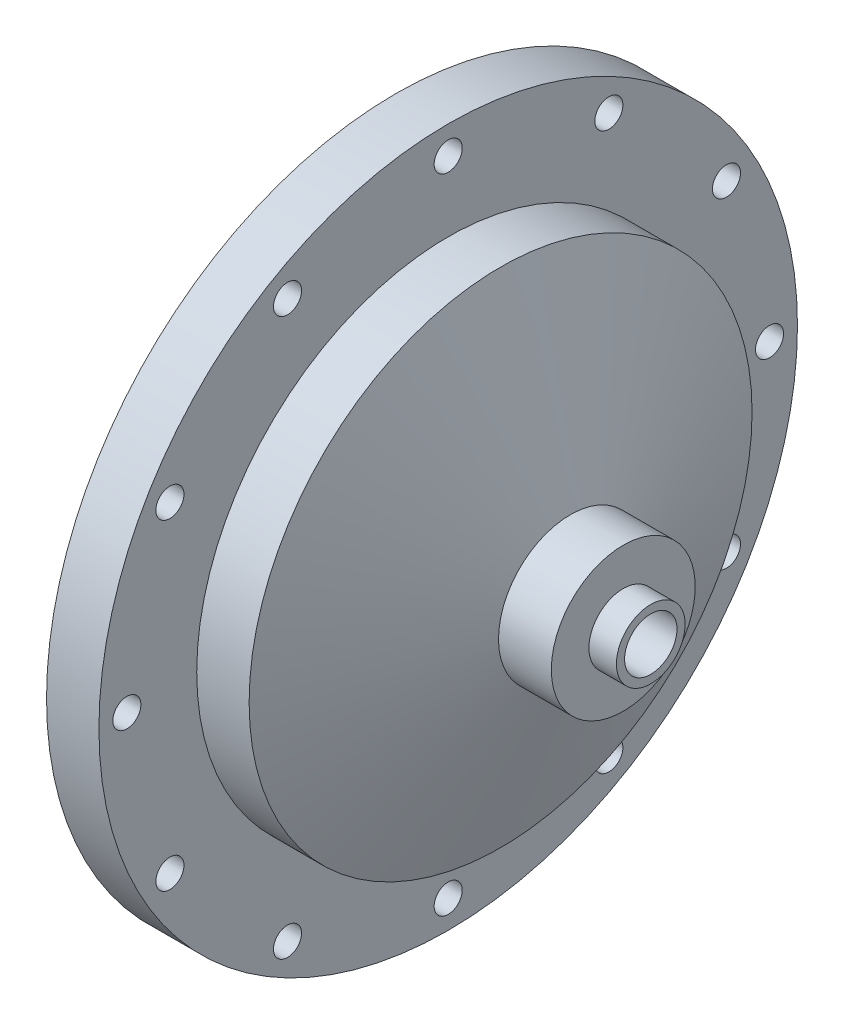
SolidWorks part; units mm, degrees
material "7075-T6 (SN)"
ref_plane "Front Plane" through (0, 0, 0) normal (0, 0, 1) x (1, 0, 0)
ref_plane "Top Plane" through (0, 0, 0) normal (0, 1, 0) x (1, 0, 0)
ref_plane "Right Plane" through (0, 0, 0) normal (1, 0, 0) x (0, 0, -1)
sketch "Sketch2" plane through (0, 0, 0) normal (0, 0, 1) x (1, 0, 0)
  line L0 (0, 0) -> (165.0115, 0) construction
  line L1 (0, 0) -> (0, 63.5)
  line L2 (0, 63.5) -> (9.525, 63.5)
  line L4 (19.05, 45.72) -> (31.75, 13.081)
  line L5 (41.355, 13.081) -> (41.355, 6.2484)
  line L6 (31.75, 13.081) -> (41.355, 13.081)
  line L7 (41.355, 6.2484) -> (46.355, 6.2484)
  line L8 (46.355, 6.2484) -> (46.355, 0)
  line L9 (0, 0) -> (46.355, 0)
  line L11 (19.05, 45.72) -> (9.525, 45.72)
  line L14 (9.525, 45.72) -> (9.525, 63.5)
  dimension "D1" = 63.5
  dimension "D2" = 9.525
  dimension "D3" = 45.72
  dimension "D4" = 13.081
  dimension "D5" = 12.7
  dimension "D7" = 6.2484
  dimension "D8" = 5
  dimension "D9" = 9.525
  dimension "D10" = 46.355
revolve "Main Structure" add sketch "Sketch2" angle 360 about L0
cosmetic thread "Cosmetic Thread1" parameters "D2"=23.1953
sketch "Sketch3" plane through (46.355, 0, 0) normal (1, 0, 0) x (0, 0, -1)
  circle A0 centre (0, 0) radius 4.7625
  dimension "D1" = 9.525
extrude "Oxidizer Inlet Hole" cut sketch "Sketch3" against normal through all
sketch "Sketch4" plane through (0, 0, 0) normal (-1, 0, 0) x (0, 0, 1)
  circle A0 centre (0, 0) radius 58.42 construction
  circle A1 centre (0, -58.42) radius 2.146
  circle A2 centre (-29.21, -50.5932) radius 2.146
  circle A3 centre (-50.5932, -29.21) radius 2.146
  circle A4 centre (-58.42, 0) radius 2.146
  circle A5 centre (-50.5932, 29.21) radius 2.146
  circle A6 centre (-29.21, 50.5932) radius 2.146
  circle A7 centre (0, 58.42) radius 2.146
  circle A8 centre (29.21, 50.5932) radius 2.146
  circle A9 centre (50.5932, 29.21) radius 2.146
  circle A10 centre (58.42, 0) radius 2.146
  circle A11 centre (50.5932, -29.21) radius 2.146
  circle A12 centre (29.21, -50.5932) radius 2.146
  point P29 (0, 0)
  dimension "D1" = 12
  dimension "D2" = 116.84
hole_wizard "Flange Holes" positions "Sketch7" profile "Sketch8" hole size "#7" standard "ANSI Inch" end condition up to next
sketch "Sketch7" plane through (0, 0, 0) normal (-1, 0, 0) x (0, 0, 1)
  point P0 (0, -58.42)
  point P3 (-29.21, -50.5932)
  point P6 (-50.5932, -29.21)
  point P9 (-58.42, 0)
  point P12 (-50.5932, 29.21)
  point P15 (-29.21, 50.5932)
  point P18 (0, 58.42)
  point P21 (29.21, 50.5932)
  point P24 (50.5932, 29.21)
  point P27 (58.42, 0)
  point P30 (50.5932, -29.21)
  point P33 (29.21, -50.5932)
sketch "Sketch8" plane through (0, -58.42, 0) normal (0, 1, 0) x (0, 0, 1)
  line L0 (0, 0) -> (0, 9.525)
  line L1 (0, 9.525) -> (2.5527, 9.525)
  line L2 (2.5527, 9.525) -> (2.5527, 0)
  line L5 (2.5527, 0) -> (0, 0)
  line L11 (0, -6.35) -> (0, 107.95) construction
  dimension "Thru Hole Dia." = 5.1054
  dimension "Thru Hole Depth" = 9.525
sketch "Sketch9" plane through (0, 0, 0) normal (-1, 0, 0) x (0, 0, 1)
  line L0 (0, 0) -> (-67.6727, 18.1329) construction
  line L1 (0, 0) -> (-58.42, 0) construction
  circle A0 centre (0, 0) radius 58.42 construction
  circle A1 centre (-56.4294, 15.1202) radius 2.9451
  circle A2 centre (56.4294, -15.1202) radius 2.9451
  point P14 (0, 0)
  dimension "D1" = 15
  dimension "D2" = 2
hole_wizard "Dowel Holes" positions "Sketch10" profile "Sketch11" hole size "3/16" standard "ANSI Inch"
sketch "Sketch10" plane through (0, 0, 0) normal (-1, 0, 0) x (0, 0, 1)
  point P0 (56.4294, -15.1202)
  point P3 (-56.4294, 15.1202)
sketch "Sketch11" plane through (0, -15.1202, 56.4294) normal (0, 1, 0) x (0, 0, 1)
  line L0 (0, 0) -> (0, 7.7808)
  line L1 (0, 7.7808) -> (2.3812, 6.35)
  line L2 (2.3812, 6.35) -> (2.3812, 0)
  line L5 (2.3812, 0) -> (0, 0)
  line L10 (0, 7.7808) -> (-2.3812, 6.35) construction
  line L11 (0, -6.35) -> (0, 107.95) construction
  dimension "Hole Dia." = 4.7625
  dimension "Hole Depth" = 6.35
  dimension "Drill Angle" = 118
sketch "Sketch12" plane through (0, 0, 0) normal (-1, 0, 0) x (0, 0, 1)
  circle A0 centre (0, 0) radius 38.1
  dimension "D1" = 76.2
extrude "Impinging Plate Flat Cut" cut sketch "Sketch12" against normal blind 3.81
ref_plane "Plane1" through (6.35, 0, 0) normal (-1, 0, 0) x (0, 0, 1)
sketch "Sketch14" plane through (3.81, 0, 0) normal (-1, 0, 0) x (0, 0, 1)
  circle A0 centre (0, 0) radius 38.1
  dimension "D1" = 76.2
sketch "Sketch15" plane through (6.35, 0, 0) normal (-1, 0, 0) x (0, 0, 1)
  circle A0 centre (0, 0) radius 38.1
  dimension "D1" = 76.2
ref_plane "Plane4" through (15.875, 0, 0) normal (-1, 0, 0) x (0, 0, 1)
loft "Impinging Plate Taper Cut" cut profiles "Sketch14", "Sketch15"
sketch "Sketch16" plane through (15.875, 0, 0) normal (-1, 0, 0) x (0, 0, 1)
  circle A0 centre (0, 0) radius 28.575
  dimension "D1" = 57.15
ref_plane "Plane2" through (31.115, 0, 0) normal (-1, 0, 0) x (0, 0, 1)
sketch "Sketch17" plane through (31.115, 0, 0) normal (-1, 0, 0) x (0, 0, 1)
  circle A0 centre (0, 0) radius 4.7625
  dimension "D1" = 9.525
loft "Internal Flow Path Loft Cut" cut profiles "Sketch16", "Sketch17"
sketch "Sketch21" plane through (6.35, 0, 0) normal (-1, 0, 0) x (0, 0, 1)
  circle A0 centre (0, 0) radius 28.575
  dimension "D1" = 57.15
extrude "Cut-Extrude1" cut sketch "Sketch21" against normal blind 9.525
fillet "Internal Fillet" radius 3.175 1 edges at (31.115, 0, 4.7625)
sketch "Sketch18" plane through (6.35, 0, 0) normal (-1, 0, 0) x (0, 0, 1)
  circle A0 centre (0, 0) radius 33.3375
  circle A1 centre (33.3375, 0) radius 1.5042
  dimension "D1" = 66.675
hole_wizard "4-40 Tapped Holes " positions "Sketch19" profile "Sketch20" tap size "#4-40" standard "ANSI Inch"
sketch "Sketch19" plane through (6.35, 0, 0) normal (-1, 0, 0) x (0, 0, 1)
  point P0 (33.3375, 0)
sketch "Sketch20" plane through (6.35, 0, 33.3375) normal (0, 1, 0) x (0, 0, 1)
  line L0 (0, 0) -> (0, 13.8872)
  line L1 (0, 13.8872) -> (1.1303, 13.208)
  line L2 (1.1303, 13.208) -> (1.1303, 0)
  line L5 (1.1303, 0) -> (0, 0)
  line L10 (0, 13.8872) -> (-1.1303, 13.208) construction
  line L11 (0, -6.35) -> (0, 107.95) construction
  dimension "Tap Drill Dia." = 2.2606
  dimension "Tap Drill Depth" = 13.208
  dimension "Drill Angle" = 118
cosmetic thread "Hole Thread1" parameters "D1"=9.906, "D2"=2.8448
pattern_circular "Extended 8 BC" count 8 over 360 about axis through (0, 0, 0) along (1, 0, 0) of "4-40 Tapped Holes "
chamfer "Chamfer for Impinging Edge" distance 0.127 angle 45 1 edges at (6.35, 0, 38.1)
